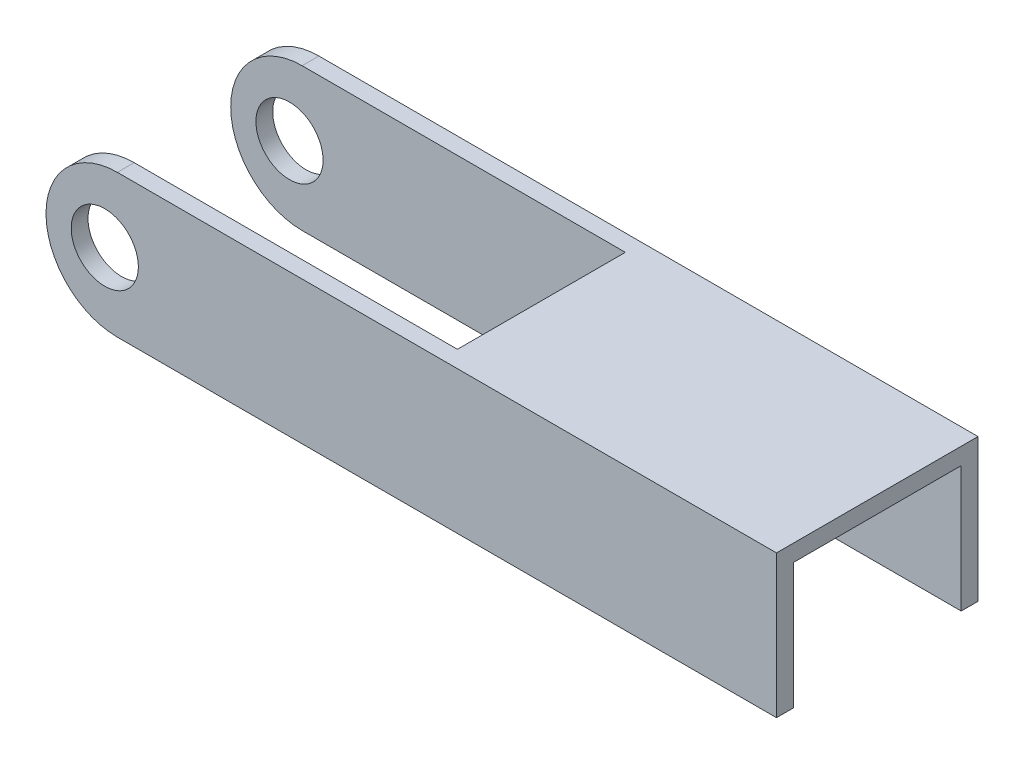
SolidWorks part; units mm, degrees
ref_plane "前视基准面" through (0, 0, 0) normal (0, 0, 1) x (1, 0, 0)
ref_plane "上视基准面" through (0, 0, 0) normal (0, 1, 0) x (1, 0, 0)
ref_plane "右视基准面" through (0, 0, 0) normal (1, 0, 0) x (0, 0, -1)
sketch "草图1" plane through (0, 0, 0) normal (0, 0, 1) x (1, 0, 0)
  line L1 (-4.3035, 8.6715) -> (4.1965, 8.6715)
  line L2 (4.1965, 8.6715) -> (74.1965, 8.6715)
  line L3 (74.1965, 8.6715) -> (74.1965, -8.3285)
  line L4 (74.1965, -8.3285) -> (-4.3035, -8.3285)
  line L5 (-12.8035, 0.1715) -> (-5.8035, 0.1715) construction
  circle A0 centre (-5.8035, 0.1715) radius 4
  arc A1 (-4.3035, 8.6715) -> (-4.3035, -8.3285) centre (-4.3035, 0.1715) ccw
  dimension "D3" = 70
  dimension "D4" = 7
extrude "凸台-拉伸1" add sketch "草图1" along normal blind 2
sketch "草图2" plane through (0, 0, 0) normal (0, 0, -1) x (-1, 0, 0)
  line L0 (-74.1965, 8.6715) -> (-34.1965, 8.6715)
  line L1 (-74.1965, 8.6715) -> (4.3035, 8.6715) construction
  line L2 (-34.1965, 8.6715) -> (-34.1965, 6.6715)
  line L3 (-34.1965, 6.6715) -> (-74.1965, 6.6715)
  line L4 (-74.1965, -8.3285) -> (-74.1965, 8.6715) construction
  line L5 (-74.1965, 6.6715) -> (-74.1965, 8.6715)
  dimension "D1" = 40
  dimension "D2" = 2
extrude "凸台-拉伸2" add sketch "草图2" along normal blind 20
ref_plane "基准面1" through (0, 0, -10) normal (0, 0, -1) x (-1, 0, 0)
mirror "镜向1" about plane through (0, 0, -10) normal (0, 0, -1) of "凸台-拉伸1"
